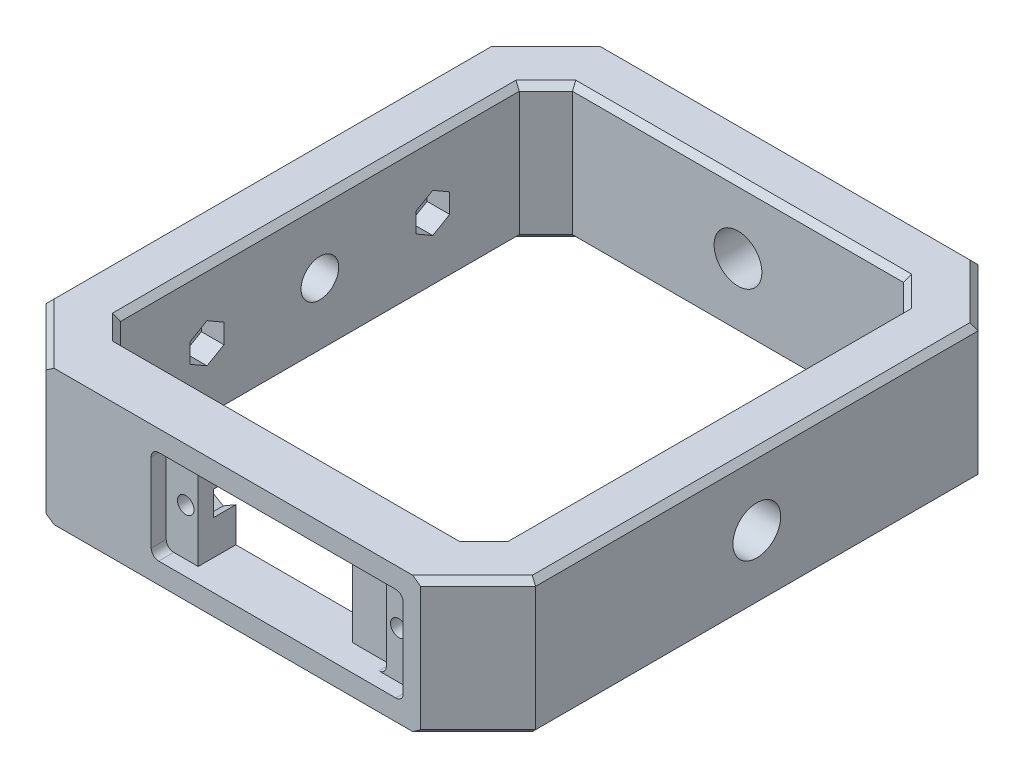
SolidWorks part; units mm, degrees
ref_plane "Front" through (0, 0, 0) normal (0, 0, 1) x (1, 0, 0)
ref_plane "Top" through (0, 0, 0) normal (0, 1, 0) x (1, 0, 0)
ref_plane "Right" through (0, 0, 0) normal (1, 0, 0) x (0, 0, -1)
sketch "Sketch1" plane through (0, 0, 0) normal (0, 1, 0) x (1, 0, 0)
  line L0 (-25.5355, 26.5) -> (-22, 30.0355)
  line L1 (-22, 30.0355) -> (22, 30.0355)
  line L2 (-25.5355, 26.5) -> (-25.5355, -26.5)
  line L3 (-22, -30.0355) -> (22, -30.0355)
  line L4 (25.5355, 26.5) -> (25.5355, -26.5)
  line L5 (-25.5355, 0) -> (25.5355, 0) construction
  line L6 (0, 30.0355) -> (0, -30.0355) construction
  line L7 (-25.5355, -26.5) -> (-22, -30.0355)
  line L8 (22, 30.0355) -> (25.5355, 26.5)
  line L9 (22, -30.0355) -> (25.5355, -26.5)
  line L10 (-32.5355, 29.3995) -> (-32.5355, -29.3995)
  line L11 (-32.5355, -29.3995) -> (-24.8995, -37.0355)
  line L12 (-24.8995, -37.0355) -> (24.8995, -37.0355)
  line L13 (24.8995, -37.0355) -> (32.5355, -29.3995)
  line L14 (32.5355, 29.3995) -> (32.5355, -29.3995)
  line L15 (24.8995, 37.0355) -> (32.5355, 29.3995)
  line L16 (-24.8995, 37.0355) -> (24.8995, 37.0355)
  line L17 (-32.5355, 29.3995) -> (-24.8995, 37.0355)
  point P1 (0, 0)
  point P5 (0, 0)
  dimension "D2" = 53
  dimension "D3" = 45
  dimension "D4" = 5
  dimension "D5" = 45
  dimension "D6" = 5
  dimension "D7" = 5
  dimension "D8" = 45
  dimension "D9" = 45
  dimension "D10" = 5
  dimension "D12" = 44
  dimension "D11" = 7
extrude "Boss-Extrude1" add sketch "Sketch1" along normal mid plane 18
sketch "Sketch11" plane through (32.5355, 0, 0) normal (1, 0, 0) x (0, 0, -1)
  line L0 (-29.3995, 0) -> (29.3995, 0) construction
  line L1 (-29.3995, 9) -> (-29.3995, -9) construction
  line L2 (29.3995, 9) -> (29.3995, -9) construction
  circle A0 centre (0, 0) radius 3.175
  dimension "D1" = 6.35
extrude "Bearing Hole" cut sketch "Sketch11" against normal up to next
sketch "Sketch25" plane through (-32.5355, 0, 0) normal (-1, 0, 0) x (0, 0, 1)
  line L0 (-29.3995, 0) -> (29.3995, 0) construction
  line L1 (-29.3995, 9) -> (-29.3995, -9) construction
  line L2 (29.3995, 9) -> (29.3995, -9) construction
  line L3 (-15.25, 2.4875) -> (-0.4, 3.9799)
  line L4 (0.4, -3.9799) -> (15.25, -2.4875)
  line L5 (-15.25, -2.4875) -> (-0.4, -3.9799)
  line L6 (0.4, 3.9799) -> (15.25, 2.4875)
  line L7 (-15.35, 3.4825) -> (-0.5, 4.9749)
  line L8 (0.5, 4.9749) -> (15.35, 3.4825)
  line L9 (0.5, -4.9749) -> (15.35, -3.4825)
  line L10 (-15.35, -3.4825) -> (-0.5, -4.9749)
  arc A0 (-0.4, -3.9799) -> (0.4, -3.9799) centre (0, 0) ccw
  arc A1 (15.25, -2.4875) -> (15.25, 2.4875) centre (15, 0) ccw
  arc A2 (-15.25, 2.4875) -> (-15.25, -2.4875) centre (-15, 0) ccw
  arc A3 (0.4, 3.9799) -> (-0.4, 3.9799) centre (0, 0) ccw
  arc A4 (0.5, 4.9749) -> (-0.5, 4.9749) centre (0, 0) ccw
  arc A5 (15.35, -3.4825) -> (15.35, 3.4825) centre (15, 0) ccw
  arc A6 (-0.5, -4.9749) -> (0.5, -4.9749) centre (0, 0) ccw
  arc A7 (-15.35, 3.4825) -> (-15.35, -3.4825) centre (-15, 0) ccw
  dimension "D1" = 5
  dimension "D2" = 5
  dimension "D3" = 8
  dimension "D4" = 15
  dimension "D5" = 15
  dimension "D6" = 1
sketch "Sketch27" plane through (-32.5355, 0, 0) normal (-1, 0, 0) x (0, 0, 1)
  line L0 (-29.3995, 0) -> (29.3995, 0) construction
  line L1 (-29.3995, 9) -> (-29.3995, -9) construction
  line L2 (29.3995, 9) -> (29.3995, -9) construction
  circle A0 centre (-15, 0) radius 0.8
  circle A1 centre (15, 0) radius 0.8
  point P10 (0, 0)
  dimension "D1" = 1.6
  dimension "D2" = 1.6
  dimension "D3" = 15
  dimension "D4" = 15
extrude "Cut-Extrude23" cut sketch "Sketch27" against normal up to next
extrude "Cut-Extrude25" cut sketch "Sketch25" against normal blind 1.75 contours A2 L0 A1 L6 A3 L3 | L0 A2 L5 A0 L4 A1 | A7 L0 A2 L3 A3 L6 A1 A5 L8 A4 L7 | L0 A7 L10 A6 L9 A5 A1 L4 A0 L5 A2
sketch "Sketch28" plane through (-30.7855, 0, 0) normal (-1, 0, 0) x (0, 0, 1)
  line L0 (-15, 0) -> (15, 0) construction
  circle A0 centre (0, 0) radius 2.5
  dimension "D1" = 5
extrude "Cut-Extrude26" cut sketch "Sketch28" against normal up to next
sketch "Sketch29" plane through (0, 0, -37.0355) normal (0, 0, -1) x (-1, 0, 0)
  line L0 (-24.8995, 0) -> (24.8995, 0) construction
  line L1 (-24.8995, 9) -> (-24.8995, -9) construction
  line L2 (24.8995, 9) -> (24.8995, -9) construction
  circle A0 centre (0, 0) radius 3.175
  dimension "D1" = 6.35
extrude "Cut-Extrude27" cut sketch "Sketch29" against normal up to next
sketch "Sketch35" plane through (0, 0, 37.0355) normal (0, 0, 1) x (1, 0, 0)
  line L0 (-24.8995, 0) -> (24.8995, 0) construction
  line L1 (-24.8995, 9) -> (-24.8995, -9) construction
  line L2 (24.8995, 9) -> (24.8995, -9) construction
  line L4 (-10.92, 6.25) -> (22.58, 6.25)
  line L5 (-10.92, 6.25) -> (-10.92, -6.25)
  line L6 (-10.92, -6.25) -> (22.58, -6.25)
  line L7 (22.58, 6.25) -> (22.58, -6.25)
  line L8 (-10.92, 6.25) -> (22.58, -6.25) construction
  line L9 (-10.92, -6.25) -> (22.58, 6.25) construction
  point P6 (5.83, 0)
  dimension "D1" = 12.5
  dimension "D2" = 33.5
  dimension "D3" = 5.83
extrude "Cut-Extrude29" cut sketch "Sketch35" against normal blind 2
sketch "Sketch36" plane through (0, 0, 35.0355) normal (0, 0, 1) x (1, 0, 0)
  line L0 (-10.92, 0) -> (22.58, 0) construction
  line L1 (-10.92, 6.25) -> (-10.92, -6.25) construction
  line L2 (22.58, -6.25) -> (22.58, 6.25) construction
  line L3 (-10.92, -6.25) -> (22.58, -6.25) construction
  line L4 (-6.67, 6.25) -> (18.33, 6.25)
  line L5 (-6.67, 6.25) -> (-6.67, -6.25)
  line L6 (-6.67, -6.25) -> (18.33, -6.25)
  line L7 (18.33, 6.25) -> (18.33, -6.25)
  line L8 (-6.67, 6.25) -> (18.33, -6.25) construction
  line L9 (-6.67, -6.25) -> (18.33, 6.25) construction
  point P6 (5.83, 0)
  point P13 (5.83, 0)
  dimension "D1" = 25
extrude "Cut-Extrude30" cut sketch "Sketch36" against normal up to next
sketch "Sketch37" plane through (0, 0, 35.0355) normal (0, 0, 1) x (1, 0, 0)
  line L0 (-10.92, 0) -> (22.58, 0) construction
  line L1 (-10.92, 6.25) -> (-10.92, -6.25) construction
  line L2 (22.58, -6.25) -> (22.58, 6.25) construction
  line L3 (-7.8225, -6.25) -> (-7.8225, 6.25) construction
  line L4 (-10.92, -6.25) -> (22.58, -6.25) construction
  line L5 (22.58, 6.25) -> (-10.92, 6.25) construction
  line L6 (19.4825, 6.25) -> (19.4825, -6.25) construction
  line L7 (22.58, 6.25) -> (18.33, 6.25) construction
  line L8 (18.33, -6.25) -> (22.58, -6.25) construction
  circle A0 centre (19.9905, 0) radius 1.1
  circle A1 centre (-8.3305, 0) radius 1.1
  point P30 (5.83, 0)
  dimension "D1" = 2.2
  dimension "D2" = 2.2
  dimension "D7" = 28.321
  dimension "D8" = 27.305
  dimension "D9" = 0.508
  dimension "D14" = 14.1605
extrude "Cut-Extrude31" cut sketch "Sketch37" against normal up to next
fillet "Fillet1" radius 1 7 edges at (18.33, -6.25, 32.5355) (22.58, -6.25, 36.0355) (22.58, 6.25, 36.0355) (18.33, 6.25, 32.5355) (-6.67, 6.25, 32.5355) (-10.92, -6.25, 36.0355) (-10.92, 6.25, 36.0355)
sketch "Sketch41" plane through (0, 0, 30.0355) normal (0, 0, -1) x (-1, 0, 0)
  line L1 (-12.33, -6.25) -> (-18.33, -6.25)
  line L2 (-12.33, -6.25) -> (-12.33, 6.25)
  line L3 (-12.33, 6.25) -> (-18.33, 6.25)
  line L4 (-18.33, -6.25) -> (-18.33, 6.25)
  line L5 (-12.33, -6.25) -> (-18.33, 6.25) construction
  line L6 (-12.33, 6.25) -> (-18.33, -6.25) construction
  point P0 (-15.33, 0)
  dimension "D1" = 6
extrude "Boss-Extrude4" add sketch "Sketch41" against normal blind 3.5
sketch "Sketch42" plane through (-25.5355, 0, 0) normal (1, 0, 0) x (0, 0, -1)
  line L0 (-15, 0) -> (15, 0) construction
  line L2 (-12.75, -1.299) -> (-12.75, 1.299)
  line L3 (-12.75, 1.299) -> (-15, 2.5981)
  line L4 (-15, 2.5981) -> (-17.25, 1.299)
  line L5 (-17.25, 1.299) -> (-17.25, -1.299)
  line L6 (-17.25, -1.299) -> (-15, -2.5981)
  line L7 (-15, -2.5981) -> (-12.75, -1.299)
  line L8 (17.25, 1.299) -> (15, 2.5981)
  line L9 (15, 2.5981) -> (12.75, 1.299)
  line L10 (12.75, 1.299) -> (12.75, -1.299)
  line L11 (12.75, -1.299) -> (15, -2.5981)
  line L12 (15, -2.5981) -> (17.25, -1.299)
  line L13 (17.25, -1.299) -> (17.25, 1.299)
  circle A0 centre (-15, 0) radius 2.25 construction
  circle A1 centre (15, 0) radius 2.25 construction
  point P6 (0, 0)
  dimension "D1" = 4.5
  dimension "D2" = 4.5
extrude "Cut-Extrude32" cut sketch "Sketch42" against normal blind 3
sketch "Sketch43" plane through (0, 0, 30.0355) normal (0, 0, -1) x (-1, 0, 0)
  line L0 (-19.9905, 0) -> (8.3305, 0) construction
  line L2 (-17.7405, -1.299) -> (-17.7405, 1.299)
  line L3 (-17.7405, 1.299) -> (-19.9905, 2.5981)
  line L4 (-19.9905, 2.5981) -> (-22.2405, 1.299)
  line L5 (-22.2405, 1.299) -> (-22.2405, -1.299)
  line L6 (-22.2405, -1.299) -> (-19.9905, -2.5981)
  line L7 (-19.9905, -2.5981) -> (-17.7405, -1.299)
  line L8 (6.0805, -1.299) -> (8.3305, -2.5981)
  line L9 (8.3305, -2.5981) -> (10.5805, -1.299)
  line L10 (10.5805, -1.299) -> (10.5805, 1.299)
  line L11 (10.5805, 1.299) -> (8.3305, 2.5981)
  line L12 (8.3305, 2.5981) -> (6.0805, 1.299)
  line L13 (6.0805, 1.299) -> (6.0805, -1.299)
  circle A0 centre (-19.9905, 0) radius 2.25 construction
  circle A1 centre (8.3305, 0) radius 2.25 construction
  dimension "D1" = 4.5
  dimension "D2" = 4.5
extrude "Cut-Extrude33" cut sketch "Sketch43" against normal blind 3
chamfer "Chamfer2" distance 0.75 angle 45 28 edges at (-28.7175, -9, 33.2175) (-32.5355, -9, 0) (-28.7175, -9, -33.2175) (0, -9, -37.0355) (28.7175, -9, -33.2175) (32.5355, -9, 0) (28.7175, -9, 33.2175) (-23.7678, -9, 28.2678) (-25.5355, -9, 0) (-23.7678, -9, -28.2678) (0, -9, -30.0355) (23.7678, -9, -28.2678) (25.5355, -9, 0) (23.7678, -9, 28.2678) (23.7678, 9, 28.2678) (25.5355, 9, 0) (23.7678, 9, -28.2678) (0, 9, -30.0355) (-23.7678, 9, -28.2678) (-25.5355, 9, 0) (-23.7678, 9, 28.2678) (28.7175, 9, 33.2175) (32.5355, 9, 0) (28.7175, 9, -33.2175) (0, 9, -37.0355) (-28.7175, 9, -33.2175) (-32.5355, 9, 0) (-28.7175, 9, 33.2175)
